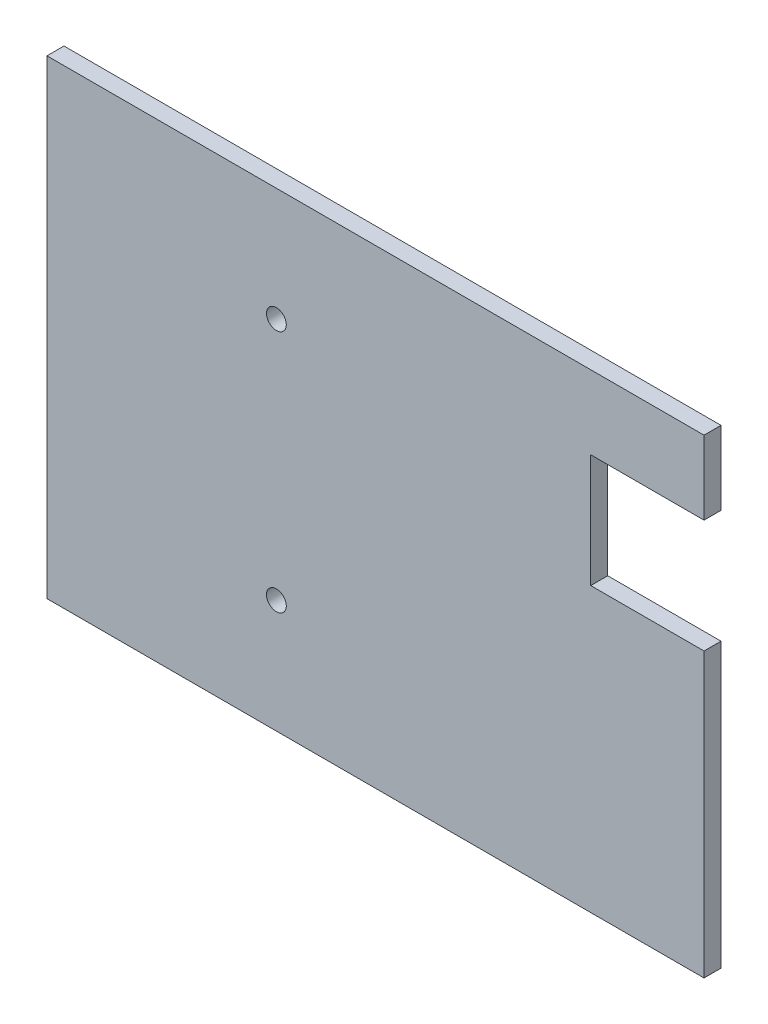
SolidWorks part; units mm, degrees
ref_plane "Front Plane" through (0, 0, 0) normal (0, 0, 1) x (1, 0, 0)
ref_plane "Top Plane" through (0, 0, 0) normal (0, 1, 0) x (1, 0, 0)
ref_plane "Right Plane" through (0, 0, 0) normal (1, 0, 0) x (0, 0, -1)
sketch "Sketch1" plane through (0, 0, 0) normal (0, 0, 1) x (1, 0, 0)
  line L1 (-73, 80) -> (-3, 80)
  line L2 (-73, 80) -> (-73, 3)
  line L3 (-73, 3) -> (-3, 3)
  line L4 (-3, 80) -> (-3, 3)
  line L5 (-113, 80) -> (-78, 80)
  line L6 (-113, 80) -> (-113, 3)
  line L7 (-113, 3) -> (-78, 3)
  line L8 (-78, 80) -> (-78, 3)
  line L9 (-116, 83) -> (0, 83)
  line L10 (-116, 83) -> (-116, 0)
  line L11 (-116, 0) -> (0, 0)
  line L12 (0, 83) -> (0, 0)
  dimension "D1" = 77
  dimension "D2" = 70
  dimension "D3" = 35
  dimension "D4" = 77
  dimension "D5" = 5
  dimension "D6" = 3
  dimension "D7" = 3
  dimension "D8" = 3
  dimension "D9" = 3
extrude "Boss-Extrude1" add sketch "Sketch1" along normal blind 3
sketch "Sketch2" plane through (0, 0, 0) normal (0, 0, -1) x (-1, 0, 0)
  line L0 (3, 3) -> (3, 80) construction
  line L1 (3, 80) -> (73, 80) construction
  line L2 (73, 80) -> (73, 3) construction
  line L3 (73, 3) -> (3, 3) construction
  line L4 (113, 3) -> (78, 3) construction
  line L5 (78, 3) -> (78, 80) construction
  line L6 (113, 80) -> (113, 3) construction
  line L7 (78, 80) -> (113, 80) construction
  line L8 (3, 3) -> (3, 80)
  line L9 (3, 80) -> (73, 80)
  line L10 (73, 80) -> (73, 3)
  line L11 (73, 3) -> (3, 3)
  line L12 (113, 3) -> (78, 3)
  line L13 (78, 3) -> (78, 80)
  line L14 (113, 80) -> (113, 3)
  line L15 (78, 80) -> (113, 80)
extrude "Boss-Extrude2" add sketch "Sketch2" against normal blind 3
sketch "Sketch6" plane through (0, 0, 3) normal (0, 0, 1) x (1, 0, 0)
  line L0 (0, 83) -> (-116, 83) construction
  line L1 (0, 0) -> (0, 83) construction
  line L4 (-116, 0) -> (0, 0) construction
  circle A0 centre (-75.5, 63) radius 1.75
  circle A1 centre (-75.5, 20) radius 1.75
  dimension "D4" = 3.5
  dimension "D5" = 3.5
  dimension "D1" = 20
  dimension "D2" = 20
  dimension "D3" = 75.5
extrude "Cut-Extrude4" cut sketch "Sketch6" against normal blind 30
sketch "Sketch8" plane through (0, 0, 3) normal (0, 0, 1) x (1, 0, 0)
  line L0 (0, 0) -> (0, 83) construction
  line L1 (0, 70) -> (-20, 70)
  line L2 (0, 70) -> (0, 50)
  line L3 (0, 50) -> (-20, 50)
  line L4 (-20, 70) -> (-20, 50)
  line L5 (0, 83) -> (-116, 83) construction
  dimension "D1" = 20
  dimension "D2" = 20
  dimension "D3" = 13
extrude "Cut-Extrude6" cut sketch "Sketch8" against normal blind 10
